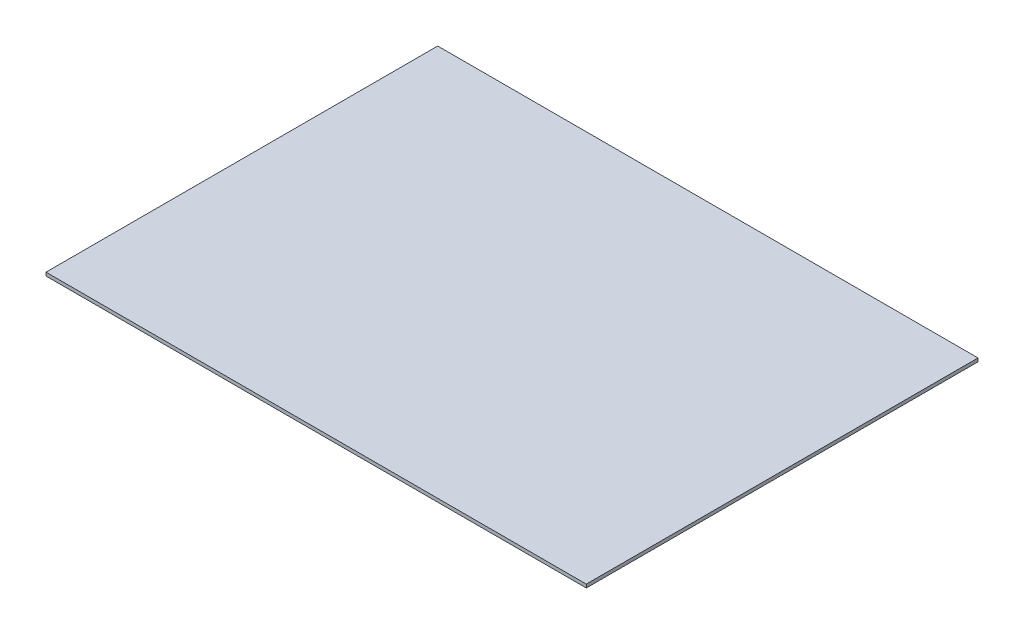
SolidWorks part; units mm, degrees
ref_plane "Front Plane" through (0, 0, 0) normal (0, 0, 1) x (1, 0, 0)
ref_plane "Top Plane" through (0, 0, 0) normal (0, 1, 0) x (1, 0, 0)
ref_plane "Right Plane" through (0, 0, 0) normal (1, 0, 0) x (0, 0, -1)
sketch "Sketch1" plane through (0, 0, 0) normal (0, 1, 0) x (1, 0, 0)
  line L1 (-10, 7.25) -> (10, 7.25)
  line L2 (-10, 7.25) -> (-10, -7.25)
  line L3 (-10, -7.25) -> (10, -7.25)
  line L4 (10, 7.25) -> (10, -7.25)
  line L5 (-10, 7.25) -> (10, -7.25) construction
  line L6 (-10, -7.25) -> (10, 7.25) construction
  point P0 (0, 0)
  dimension "D1" = 20
  dimension "D2" = 14.5
extrude "Extrude1" add sketch "Sketch1" along normal blind 0.125
